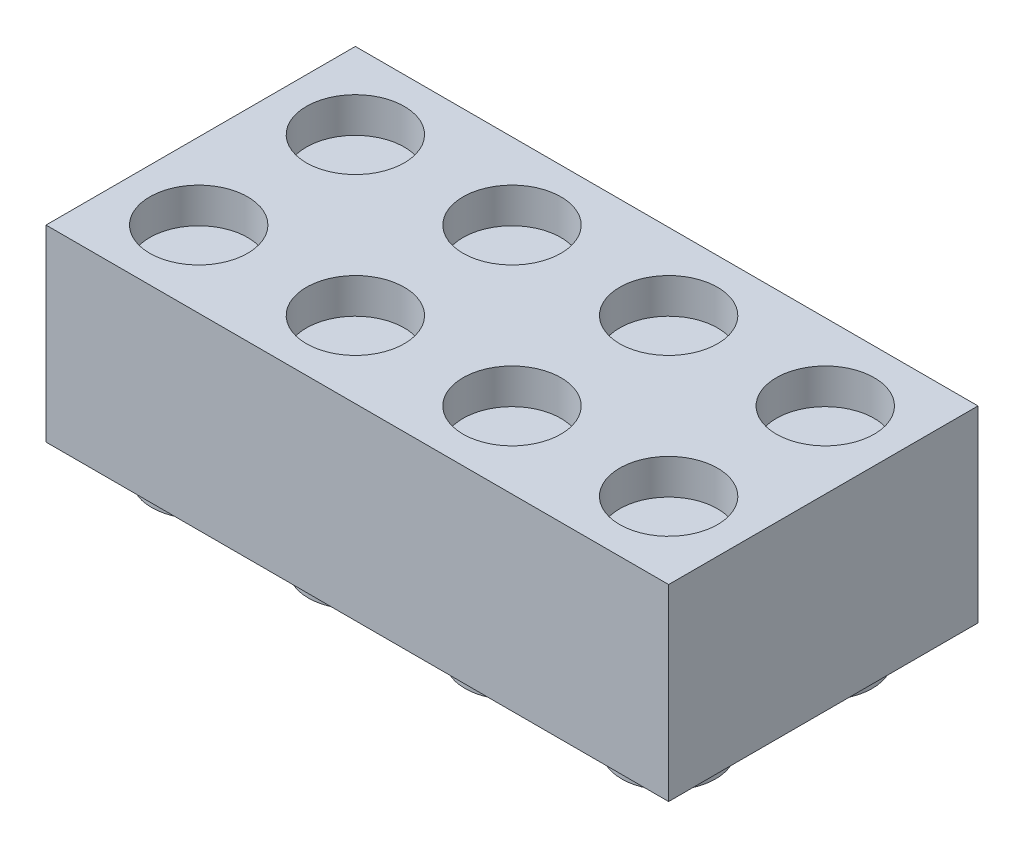
SolidWorks part; units mm, degrees
ref_plane "Спереди" through (0, 0, 0) normal (0, 0, 1) x (1, 0, 0)
ref_plane "Сверху" through (0, 0, 0) normal (0, 1, 0) x (1, 0, 0)
ref_plane "Справа" through (0, 0, 0) normal (1, 0, 0) x (0, 0, -1)
sketch "Эскиз1" plane through (0, 0, 0) normal (0, 1, 0) x (1, 0, 0)
  line L1 (0, 0) -> (31.8, 0)
  line L2 (0, 0) -> (0, 15.8)
  line L3 (0, 15.8) -> (31.8, 15.8)
  line L4 (31.8, 0) -> (31.8, 15.8)
  dimension "D1" = 31.8
  dimension "D2" = 15.8
extrude "Бобышка-Вытянуть1" add sketch "Эскиз1" along normal blind 9.6 contours L2 L1 L4 L3
sketch "Эскиз2" plane through (0, 0, 0) normal (0, -1, 0) x (1, 0, 0)
  line L0 (31.8, 0) -> (31.8, -15.8) construction
  line L1 (0, 0) -> (31.8, 0) construction
  circle A0 centre (27.9, -3.9) radius 2.4
  circle A1 centre (19.9, -3.9) radius 2.4
  circle A2 centre (11.9, -3.9) radius 2.4
  circle A3 centre (3.9, -3.9) radius 2.4
  circle A4 centre (19.9, -11.9) radius 2.4
  circle A5 centre (11.9, -11.9) radius 2.4
  circle A6 centre (3.9, -11.9) radius 2.4
  circle A7 centre (27.9, -11.9) radius 2.4
  dimension "D1" = 4.8
  dimension "D2" = 3.9
  dimension "D3" = 3.9
  dimension "D4" = 4
  dimension "D5" = 2
extrude "Бобышка-Вытянуть4" add sketch "Эскиз2" along normal blind 1.7
sketch "Эскиз3" plane through (0, 9.6, 0) normal (0, 1, 0) x (1, 0, 0)
  line L0 (0, 0) -> (31.8, 0) construction
  line L1 (31.8, 0) -> (31.8, 15.8) construction
  circle A0 centre (27.9, 3.9) radius 2.5
  circle A1 centre (19.9, 3.9) radius 2.5
  circle A2 centre (11.9, 3.9) radius 2.5
  circle A3 centre (3.9, 3.9) radius 2.5
  circle A4 centre (19.9, 11.9) radius 2.5
  circle A5 centre (11.9, 11.9) radius 2.5
  circle A6 centre (3.9, 11.9) radius 2.5
  circle A7 centre (27.9, 11.9) radius 2.5
  dimension "D1" = 5
  dimension "D2" = 3.9
  dimension "D3" = 3.9
  dimension "D4" = 4
  dimension "D5" = 2
extrude "Вырез-Вытянуть1" cut sketch "Эскиз3" against normal blind 1.8
